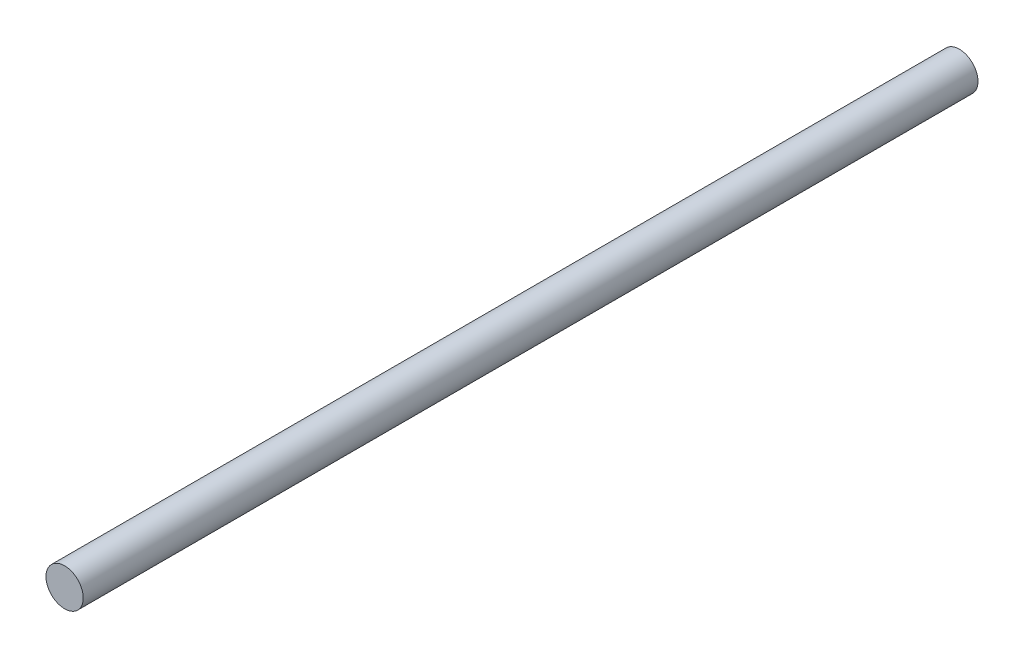
SolidWorks part; units mm, degrees
ref_plane "Plano frontal" through (0, 0, 0) normal (0, 0, 1) x (1, 0, 0)
ref_plane "Plano superior" through (0, 0, 0) normal (0, 1, 0) x (1, 0, 0)
ref_plane "Plano direito" through (0, 0, 0) normal (1, 0, 0) x (0, 0, -1)
sketch "Esboço1" plane through (0, 0, 0) normal (0, 1, 0) x (1, 0, 0)
  line L0 (0, 30) -> (0, -30)
  point P3 (0, 0)
  dimension "D1" = 60
sweep "Varredura1" add path "Esboço1" circular profile diameter 2.5 parameters "D3"=2.5
